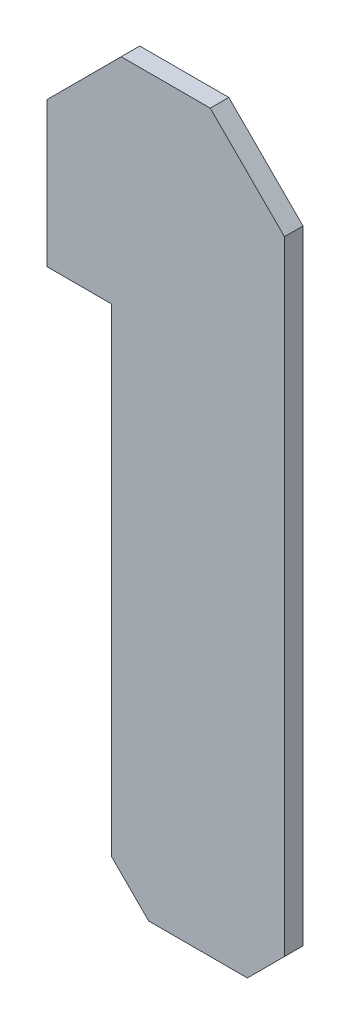
SolidWorks part; units mm, degrees
ref_plane "Front Plane" through (0, 0, 0) normal (0, 0, 1) x (1, 0, 0)
ref_plane "Top Plane" through (0, 0, 0) normal (0, 1, 0) x (1, 0, 0)
ref_plane "Right Plane" through (0, 0, 0) normal (1, 0, 0) x (0, 0, -1)
sketch "Sketch1" plane through (0, 0, 0) normal (0, 0, 1) x (1, 0, 0)
  line L0 (1.7423, -13.65) -> (2.7423, -14.65)
  line L1 (5.4, -14.65) -> (6.4, -13.65)
  line L5 (6.4, 3.15) -> (6.4, 0.1)
  line L6 (6.4, 3.15) -> (4.4, 5.15)
  line L7 (4.4, 5.15) -> (2, 5.15)
  line L8 (2, 5.15) -> (0, 3.15)
  line L9 (0, 3.15) -> (0, 0.1)
  line L10 (0, 0.1) -> (0, -0.75)
  line L11 (0, -0.75) -> (1.7423, -0.75)
  line L12 (1.7423, -0.75) -> (1.7423, -13.65)
  line L13 (2.7423, -14.65) -> (5.4, -14.65)
  line L14 (6.4, -13.65) -> (6.4, 0.1)
  point P2 (3.2, 5.15)
  point P10 (1.7423, -14.65)
  point P11 (6.4, -14.65)
  dimension "D1" = 5.05
  dimension "D2" = 5.9
  dimension "D3" = 19.8
  dimension "D4" = 1.7423
  dimension "D5" = 2
  dimension "D6" = 3.2
  dimension "D7" = 5.4
  dimension "D10" = 0.1
  dimension "D11" = 0.1
  dimension "D12" = 3.15
  dimension "D13" = 3.15
extrude "Boss-Extrude1" add sketch "Sketch1" along normal blind 0.5
